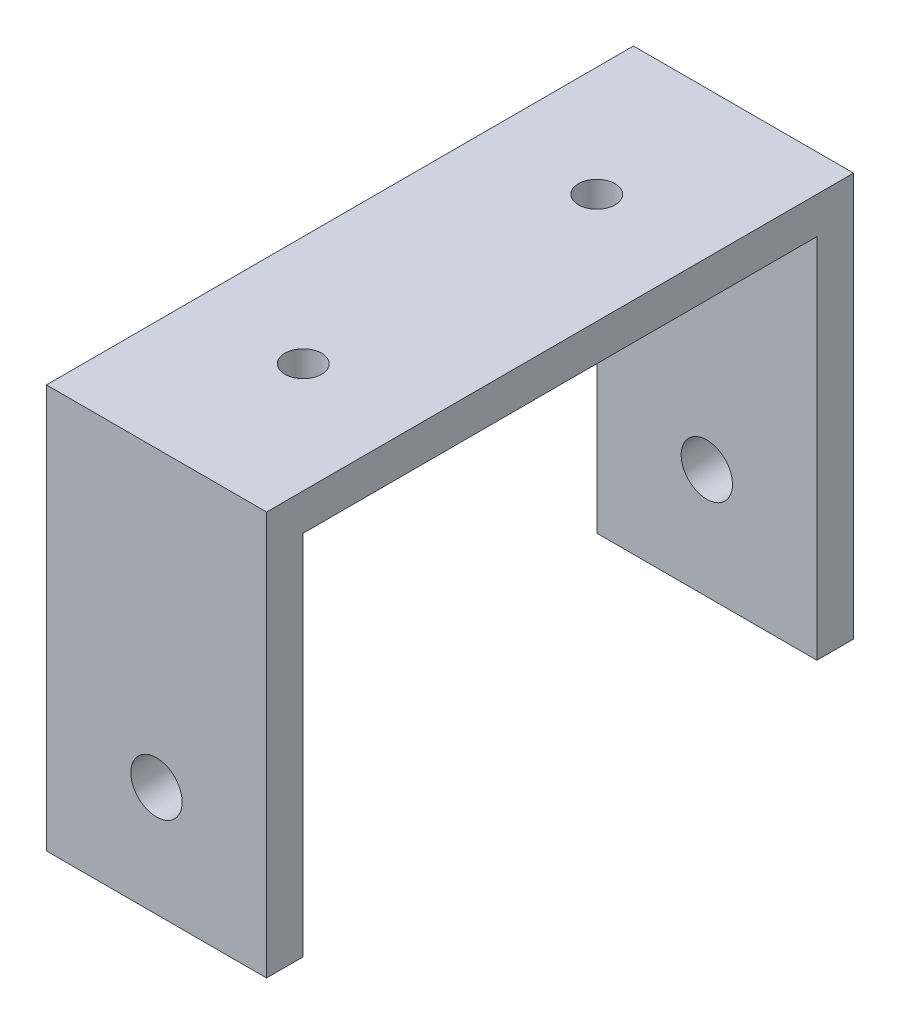
SolidWorks part; units mm, degrees
material "5052-H32"
ref_plane "Front Plane" through (0, 0, 0) normal (0, 0, 1) x (1, 0, 0)
ref_plane "Top Plane" through (0, 0, 0) normal (0, 1, 0) x (1, 0, 0)
ref_plane "Right Plane" through (0, 0, 0) normal (1, 0, 0) x (0, 0, -1)
sketch "Sketch1" plane through (0, 0, 0) normal (0, 0, 1) x (1, 0, 0)
  line L1 (-15, 27.5) -> (15, 27.5)
  line L2 (-15, 27.5) -> (-15, -27.5)
  line L3 (-15, -27.5) -> (15, -27.5)
  line L4 (15, 27.5) -> (15, -27.5)
  line L5 (-15, 27.5) -> (15, -27.5) construction
  line L6 (-15, -27.5) -> (15, 27.5) construction
  point P0 (0, 0)
  dimension "D1" = 30
  dimension "D2" = 55
extrude "Boss-Extrude1" add sketch "Sketch1" along normal blind 80
sketch "Sketch2" plane through (15, 0, 0) normal (1, 0, 0) x (0, 0, -1)
  line L0 (-75, -27.5) -> (-75, 22.5)
  line L1 (-80, -27.5) -> (0, -27.5) construction
  line L2 (-75, 22.5) -> (-5, 22.5)
  line L3 (-5, 22.5) -> (-5, -27.5)
  line L4 (-5, -27.5) -> (-75, -27.5)
  line L5 (-80, -27.5) -> (-80, 27.5) construction
  line L6 (0, -27.5) -> (0, 27.5) construction
  line L7 (-80, 27.5) -> (0, 27.5) construction
  dimension "D1" = 5
  dimension "D2" = 5
  dimension "D3" = 5
extrude "Cut-Extrude1" cut sketch "Sketch2" against normal blind 60
sketch "Sketch3" plane through (0, 0, 80) normal (0, 0, 1) x (1, 0, 0)
  line L0 (-15, -27.5) -> (15, -27.5) construction
  line L1 (-15, 27.5) -> (-15, -27.5) construction
  circle A0 centre (0, -12.5) radius 3.5
  dimension "D1" = 7
  dimension "D2" = 15
  dimension "D3" = 15
extrude "Cut-Extrude2" cut sketch "Sketch3" against normal blind 117
sketch "Sketch4" plane through (0, 0, 0) normal (0, 1, 0) x (1, 0, 0)
  line L0 (15, 0) -> (-15, 0) construction
  line L1 (15, -80) -> (-15, -80) construction
  line L2 (-15, -80) -> (-15, 0) construction
  circle A0 centre (0, -20) radius 2.5
  circle A1 centre (0, -60) radius 2.5
  dimension "D1" = 5
  dimension "D2" = 5
  dimension "D3" = 20
  dimension "D4" = 20
  dimension "D5" = 15
  dimension "D6" = 15
extrude "Cut-Extrude3" cut sketch "Sketch4" along normal blind 42
